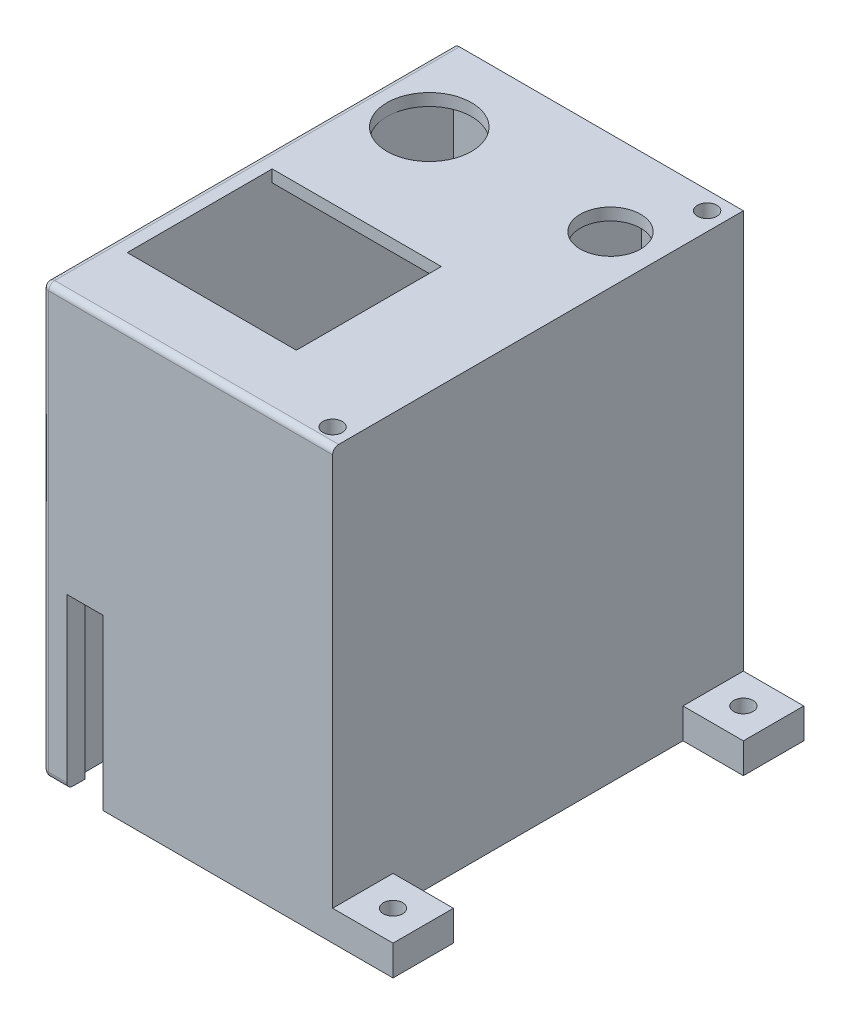
SolidWorks part; units mm, degrees
ref_plane "Front Plane" through (0, 0, 0) normal (0, 0, 1) x (1, 0, 0)
ref_plane "Top Plane" through (0, 0, 0) normal (0, 1, 0) x (1, 0, 0)
ref_plane "Right Plane" through (0, 0, 0) normal (1, 0, 0) x (0, 0, -1)
sketch "Sketch1" plane through (0, 0, 0) normal (0, 1, 0) x (1, 0, 0)
  line L1 (-23.3094, 13.3813) -> (24.6906, 13.3813)
  line L2 (-23.3094, 13.3813) -> (-23.3094, -54.6187)
  line L3 (-23.3094, -54.6187) -> (24.6906, -54.6187)
  line L4 (24.6906, 13.3813) -> (24.6906, -54.6187)
  dimension "D1" = 48
  dimension "D2" = 68
extrude "Boss-Extrude1" add sketch "Sketch1" along normal blind 71
sketch "Sketch2" plane through (0, 0, 0) normal (0, -1, 0) x (1, 0, 0)
  line L0 (-23.3094, 54.6187) -> (24.6906, 54.6187) construction
  line L1 (-20.3094, 51.6187) -> (21.6906, 51.6187)
  line L2 (-20.3094, 51.6187) -> (-20.3094, -10.3813)
  line L3 (-20.3094, -10.3813) -> (21.6906, -10.3813)
  line L4 (21.6906, 51.6187) -> (21.6906, -10.3813)
  line L5 (-23.3094, -13.3813) -> (-23.3094, 54.6187) construction
  line L6 (24.6906, -13.3813) -> (-23.3094, -13.3813) construction
  line L7 (24.6906, 54.6187) -> (24.6906, -13.3813) construction
  dimension "D1" = 3
  dimension "D2" = 3
  dimension "D3" = 3
  dimension "D4" = 3
extrude "Cut-Extrude1" cut sketch "Sketch2" against normal blind 69
sketch "Sketch3" plane through (0, 71, 0) normal (0, 1, 0) x (1, 0, 0)
  line L0 (-23.3094, 13.3813) -> (-23.3094, -54.6187) construction
  line L1 (7.6906, -19.6187) -> (-20.3094, -19.6187)
  line L2 (7.6906, -19.6187) -> (7.6906, -43.6187)
  line L3 (7.6906, -43.6187) -> (-20.3094, -43.6187)
  line L4 (-20.3094, -19.6187) -> (-20.3094, -43.6187)
  line L5 (24.6906, 13.3813) -> (-23.3094, 13.3813) construction
  line L6 (24.6906, -54.6187) -> (24.6906, 13.3813) construction
  circle A0 centre (-13.3094, -0.6187) radius 7
  circle A1 centre (16.6906, -0.6187) radius 5
  dimension "D1" = 10
  dimension "D7" = 8
  dimension "D8" = 14
  dimension "D2" = 14
  dimension "D3" = 33
  dimension "D4" = 3
  dimension "D5" = 28
  dimension "D6" = 24
extrude "Cut-Extrude2" cut sketch "Sketch3" against normal blind 3
sketch "Sketch4" plane through (0, 0, -13.3813) normal (0, 0, -1) x (-1, 0, 0)
  line L0 (23.3094, 71) -> (23.3094, 0) construction
  line L1 (13.3094, 0) -> (19.3094, 0)
  line L2 (13.3094, 0) -> (13.3094, 42)
  line L3 (13.3094, 42) -> (19.3094, 42)
  line L4 (19.3094, 0) -> (19.3094, 42)
  line L5 (-24.6906, 0) -> (23.3094, 0) construction
  line L6 (-24.6906, 71) -> (23.3094, 71) construction
  point P6 (16.3094, 0)
  dimension "D1" = 4
  dimension "D2" = 0
  dimension "D3" = 6
  dimension "D4" = 29
extrude "Cut-Extrude3" cut sketch "Sketch4" against normal blind 3
sketch "Sketch5" plane through (0, 0, 54.6187) normal (0, 0, 1) x (1, 0, 0)
  line L0 (-23.3094, 71) -> (24.6906, 71) construction
  line L1 (-13.3094, 28) -> (-19.3094, 28)
  line L2 (-13.3094, 28) -> (-13.3094, 0)
  line L3 (-13.3094, 0) -> (-19.3094, 0)
  line L4 (-19.3094, 28) -> (-19.3094, 0)
  line L5 (-23.3094, 71) -> (-23.3094, 0) construction
  line L6 (-23.3094, 0) -> (24.6906, 0) construction
  dimension "D1" = 43
  dimension "D2" = 4
  dimension "D3" = 6
  dimension "D4" = 6
  dimension "D5" = 0
  dimension "D6" = 28
extrude "Cut-Extrude4" cut sketch "Sketch5" against normal blind 3
sketch "Sketch6" plane through (0, 69, 0) normal (0, -1, 0) x (1, 0, 0)
  line L0 (-20.3094, -10.3813) -> (21.6906, -10.3813) construction
  line L1 (10.8329, 51.6187) -> (7.8329, 51.6187)
  line L2 (10.8329, 51.6187) -> (10.8329, -10.3813)
  line L3 (10.8329, -10.3813) -> (7.8329, -10.3813)
  line L4 (7.8329, 51.6187) -> (7.8329, -10.3813)
  line L5 (21.6906, 51.6187) -> (-13.3094, 51.6187) construction
  line L6 (-20.3094, 19.6187) -> (-20.3094, 0.6187) construction
  point P6 (9.3329, 51.6187)
  dimension "D1" = 3
  dimension "D2" = 0
extrude "Boss-Extrude2" add sketch "Sketch6" along normal blind 69
sketch "Sketch7" plane through (-23.3094, 0, 0) normal (-1, 0, 0) x (0, 0, 1)
  line L0 (54.6187, 71) -> (54.6187, 0) construction
  line L1 (-13.3813, 71) -> (54.6187, 71) construction
  circle A0 centre (47.6187, 63) radius 1.5
  dimension "D1" = 7
  dimension "D2" = 8
extrude "Cut-Extrude5" cut sketch "Sketch7" against normal blind 3
sketch "Sketch11" plane through (0, 71, 0) normal (0, 1, 0) x (1, 0, 0)
  line L0 (24.6906, -54.6187) -> (24.6906, 13.3813) construction
  line L1 (24.6906, 13.3813) -> (-23.3094, 13.3813) construction
  line L2 (19.0449, 13.3813) -> (24.6906, 13.3813)
  line L3 (24.6906, 13.3813) -> (24.6906, 7.7355)
  arc A0 (19.0449, 13.3813) -> (24.6906, 7.7355) centre (21.6906, 10.3813) ccw
  circle A1 centre (21.6906, 10.3813) radius 1.6
  dimension "D1" = 3
  dimension "D2" = 3
extrude "Boss-Extrude3" add sketch "Sketch11" against normal blind 71
sketch "Sketch12" plane through (0, 71, 0) normal (0, 1, 0) x (1, 0, 0)
  line L0 (24.6906, -54.6187) -> (24.6906, 13.3813) construction
  line L1 (24.6906, 13.3813) -> (-23.3094, 13.3813) construction
  circle A0 centre (21.6906, 10.3813) radius 1.6
  dimension "D1" = 3
  dimension "D2" = 3
extrude "Cut-Extrude6" cut sketch "Sketch12" against normal blind 71
sketch "Sketch13" plane through (0, 71, 0) normal (0, 1, 0) x (1, 0, 0)
  line L0 (24.6906, -54.6187) -> (24.6906, 13.3813) construction
  line L2 (-23.3094, -54.6187) -> (24.6906, -54.6187) construction
  line L3 (19.0449, -54.6187) -> (24.6906, -54.6187)
  line L4 (24.6906, -54.6187) -> (24.6906, -48.973)
  arc A1 (24.6906, -48.973) -> (19.0449, -54.6187) centre (21.6906, -51.6187) ccw
  dimension "D1" = 3
  dimension "D2" = 3
extrude "Boss-Extrude4" add sketch "Sketch13" against normal blind 71
sketch "Sketch14" plane through (0, 71, 0) normal (0, 1, 0) x (1, 0, 0)
  line L0 (24.6906, -54.6187) -> (24.6906, 13.3813) construction
  line L2 (-23.3094, -54.6187) -> (24.6906, -54.6187) construction
  circle A0 centre (21.6906, -51.6187) radius 1.6
  dimension "D1" = 3
  dimension "D2" = 3
extrude "Cut-Extrude7" cut sketch "Sketch14" against normal blind 71
fillet "Fillet2" radius 1 1 edges at (0.6906, 71, 54.6187)
fillet "Fillet3" radius 1 3 edges at (-23.3094, 71, 20.1187) (-23.3094, 70.7071, 54.3258) (-23.3094, 35, 54.6187)
fillet "Fillet5" radius 1 3 edges at (-20.8094, 0, 54.6187) (-23.0165, 0, 54.3258) (-23.3094, 0, 20.1187)
sketch "Sketch17" plane through (24.6906, 0, 0) normal (1, 0, 0) x (0, 0, -1)
  line L1 (-54.6187, 0) -> (-44.6187, 0)
  line L2 (-54.6187, 0) -> (-54.6187, 5)
  line L3 (-54.6187, 5) -> (-44.6187, 5)
  line L4 (-44.6187, 0) -> (-44.6187, 5)
  dimension "D1" = 10
  dimension "D2" = 5
extrude "Boss-Extrude5" add sketch "Sketch17" along normal blind 10
sketch "Sketch18" plane through (0, 5, 0) normal (0, 1, 0) x (1, 0, 0)
  line L0 (34.6906, -44.6187) -> (34.6906, -54.6187) construction
  line L1 (34.6906, -44.6187) -> (24.6906, -44.6187) construction
  circle A0 centre (29.6906, -49.6187) radius 1.6
  dimension "D1" = 5
  dimension "D2" = 5
extrude "Cut-Extrude8" cut sketch "Sketch18" against normal blind 5
sketch "Sketch19" plane through (24.6906, 0, 0) normal (1, 0, 0) x (0, 0, -1)
  line L1 (13.3813, 0) -> (3.3813, 0)
  line L2 (13.3813, 0) -> (13.3813, 5)
  line L3 (13.3813, 5) -> (3.3813, 5)
  line L4 (3.3813, 0) -> (3.3813, 5)
  dimension "D1" = 10
  dimension "D2" = 5
extrude "Boss-Extrude6" add sketch "Sketch19" along normal blind 10
sketch "Sketch20" plane through (0, 5, 0) normal (0, 1, 0) x (1, 0, 0)
  line L0 (34.6906, 13.3813) -> (34.6906, 3.3813) construction
  line L1 (34.6906, 13.3813) -> (24.6906, 13.3813) construction
  circle A0 centre (29.6906, 8.3813) radius 1.6
  dimension "D1" = 5
  dimension "D2" = 5
extrude "Cut-Extrude10" cut sketch "Sketch20" against normal blind 5
